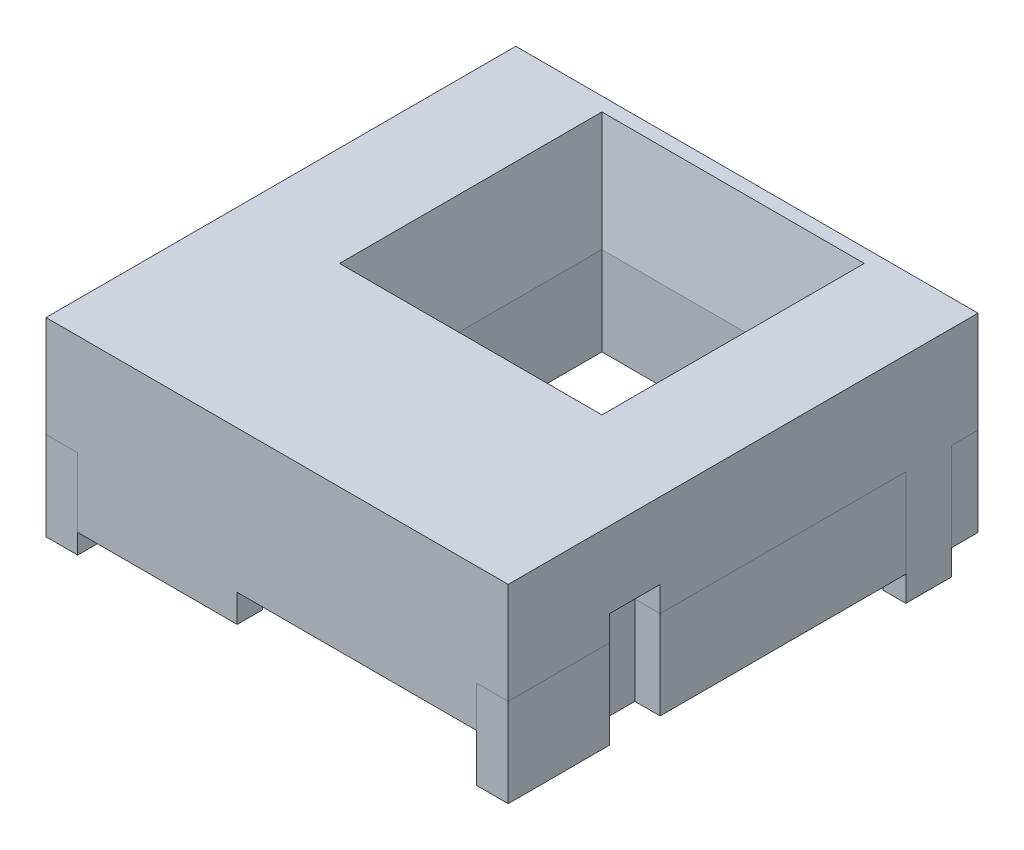
SolidWorks part; units mm, degrees
ref_plane "Front Plane" through (0, 0, 0) normal (0, 0, 1) x (1, 0, 0)
ref_plane "Top Plane" through (0, 0, 0) normal (0, 1, 0) x (1, 0, 0)
ref_plane "Right Plane" through (0, 0, 0) normal (1, 0, 0) x (0, 0, -1)
sketch "Sketch1" plane through (0, 0, 0) normal (0, 1, 0) x (1, 0, 0)
  line L1 (0, 0) -> (36.5, 0)
  line L2 (0, 0) -> (0, -37.1)
  line L3 (0, -37.1) -> (36.5, -37.1)
  line L4 (36.5, 0) -> (36.5, -37.1)
  dimension "D1" = 37.1
  dimension "D2" = 36.5
extrude "Body" add sketch "Sketch1" along normal blind 8
sketch "Sketch2" plane through (0, 0, 0) normal (0, -1, 0) x (-1, 0, 0)
  line L0 (-36.5, 0) -> (0, 0) construction
  line L1 (0, -6.1) -> (-2, -6.1)
  line L2 (0, -6.1) -> (0, -2.1)
  line L3 (0, -2.1) -> (-2, -2.1)
  line L4 (-2, -6.1) -> (-2, -2.1)
  line L5 (-34.5, -29.1) -> (-36.5, -29.1)
  line L6 (-34.5, -29.1) -> (-34.5, -25.1)
  line L7 (-34.5, -25.1) -> (-36.5, -25.1)
  line L8 (-36.5, -29.1) -> (-36.5, -25.1)
  line L10 (0, 0) -> (0, -37.1) construction
  line L11 (0, -37.1) -> (-36.5, -37.1) construction
  line L13 (-36.5, -37.1) -> (-36.5, 0) construction
  point P10 (-1, -2.1)
  dimension "D1" = 2.1
  dimension "D2" = 4
  dimension "D3" = 2
  dimension "D4" = 8
  dimension "D5" = 4
  dimension "D6" = 2
extrude "Female Tabs" cut sketch "Sketch2" against normal blind 2
sketch "Sketch3" plane through (0, 0, 0) normal (0, -1, 0) x (-1, 0, 0)
  line L0 (-36.5, -29.1) -> (-34.5, -29.1) construction
  line L1 (0, -29.1) -> (-1.8, -29.1)
  line L2 (0, -29.1) -> (0, -25.5)
  line L3 (0, -25.5) -> (-1.8, -25.5)
  line L4 (-1.8, -29.1) -> (-1.8, -25.5)
  line L5 (-34.7, -5.7) -> (-36.5, -5.7)
  line L6 (-34.7, -5.7) -> (-34.7, -2.1)
  line L7 (-34.7, -2.1) -> (-36.5, -2.1)
  line L8 (-36.5, -5.7) -> (-36.5, -2.1)
  line L9 (0, -6.1) -> (0, -37.1) construction
  line L10 (-36.5, -25.1) -> (-36.5, 0) construction
  line L11 (0, -2.1) -> (-2, -2.1) construction
  dimension "D1" = 1.8
  dimension "D2" = 3.6
  dimension "D3" = 1.8
  dimension "D4" = 3.6
extrude "Male Tabs" add sketch "Sketch3" along normal blind 9
sketch "Sketch5" plane through (0, 0, 0) normal (0, -1, 0) x (-1, 0, 0)
  line L0 (-36.5, 0) -> (0, 0) construction
  line L1 (-27.2, -2.5) -> (-9.3, -2.5)
  line L2 (-27.2, -2.5) -> (-27.2, -20.4)
  line L3 (-27.2, -20.4) -> (-9.3, -20.4)
  line L4 (-9.3, -2.5) -> (-9.3, -20.4)
  line L5 (-36.5, -2.1) -> (-36.5, 0) construction
  line L6 (0, -6.1) -> (0, -25.5) construction
  line L7 (0, -37.1) -> (-36.5, -37.1) construction
  dimension "D1" = 2.5
  dimension "D2" = 9.3
  dimension "D3" = 9.3
  dimension "D4" = 16.7
extrude "SiPM Window" cut sketch "Sketch5" against normal up to next (8 mm away) draft 10 draft outward yes
sketch "Sketch6" plane through (0, 0, 0) normal (0, -1, 0) x (1, 0, 0)
  line L0 (36.5, 0) -> (0, 0) construction
  line L1 (34, 1.5) -> (29.2, 1.5)
  line L2 (34, 1.5) -> (34, 35.1)
  line L4 (29.2, 1.5) -> (29.2, 22.4)
  line L5 (29.2, 22.4) -> (7.3, 22.4)
  line L9 (7.3, 1.5) -> (2.5, 1.5)
  line L10 (7.3, 1.5) -> (7.3, 22.4)
  line L13 (36.5, 25.1) -> (36.5, 5.7) construction
  line L16 (34, 35.1) -> (2.5, 35.1)
  line L17 (2.5, 35.1) -> (2.5, 1.5)
  line L18 (0, 6.1) -> (0, 25.5) construction
  line L19 (0, 37.1) -> (36.5, 37.1) construction
  line L20 (27.2, 20.4) -> (9.3, 20.4) construction
  line L21 (9.3, 20.4) -> (9.3, 2.5) construction
  line L22 (27.2, 2.5) -> (27.2, 20.4) construction
  dimension "D1" = 1.5
  dimension "D2" = 1.5
  dimension "D3" = 2.5
  dimension "D4" = 2.5
  dimension "D5" = 2
  dimension "D6" = 2
  dimension "D7" = 2
  dimension "D8" = 2
extrude "Cut-Extrude2" cut sketch "Sketch6" against normal offset from surface (6 mm away) 2 up to face at (18.25, 8, 11.45)
sketch "Sketch7" plane through (0, 0, 0) normal (0, -1, 0) x (1, 0, 0)
  line L0 (0, 37.1) -> (36.5, 37.1) construction
  line L1 (34, 35.1) -> (15.1, 35.1)
  line L2 (34, 35.1) -> (34, 37.1)
  line L3 (34, 37.1) -> (15.1, 37.1)
  line L4 (15.1, 35.1) -> (15.1, 37.1)
  line L5 (0, 29.1) -> (0, 37.1) construction
  dimension "D1" = 15.1
extrude "Right Drop" add sketch "Sketch7" along normal blind 3.24
sketch "Sketch8" plane through (0, 0, 0) normal (0, -1, 0) x (1, 0, 0)
  line L1 (15.1, 37.1) -> (2.5, 37.1)
  line L2 (15.1, 37.1) -> (15.1, 35.1)
  line L3 (15.1, 35.1) -> (2.5, 35.1)
  line L4 (2.5, 37.1) -> (2.5, 35.1)
extrude "Left Drop" add sketch "Sketch8" along normal blind 5.44
surface "Surface-Extrude1" parameters "D1"=7
